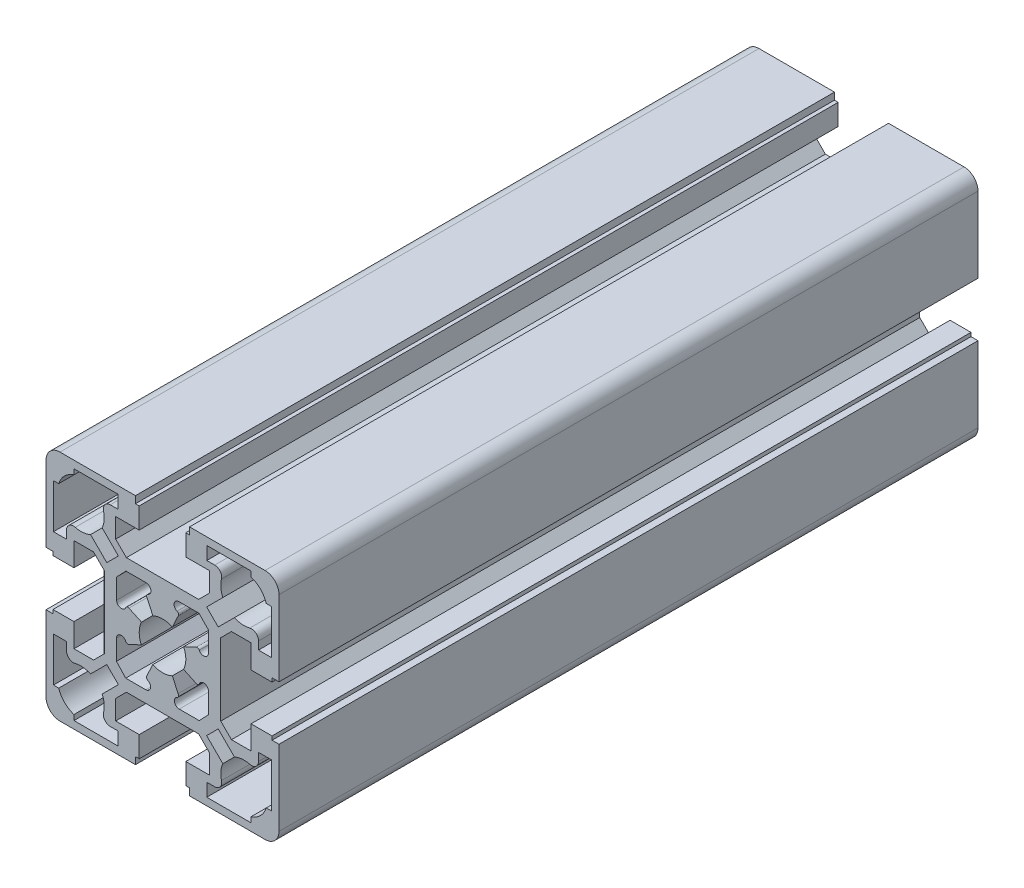
SolidWorks part; units mm, degrees
material "6063-T6"
ref_plane "Front Plane" through (0, 0, 0) normal (0, 0, 1) x (1, 0, 0)
ref_plane "Top Plane" through (0, 0, 0) normal (0, 1, 0) x (1, 0, 0)
ref_plane "Right Plane" through (0, 0, 0) normal (1, 0, 0) x (0, 0, -1)
sketch "Sketch1" plane through (0, 0, 0) normal (0, 0, 1) x (1, 0, 0)
  line L0 (3.5053, 9.9658) -> (7.8227, 9.9658)
  line L1 (7.75, 12.5) -> (-7.75, 12.5)
  line L2 (7.9026, -9.9658) -> (3.5852, -9.9658)
  line L3 (-7.75, -12.5) -> (7.75, -12.5)
  line L4 (10.05, -19) -> (5, -19)
  line L5 (5.8, -25) -> (22, -25)
  line L6 (22, 25) -> (5.8, 25)
  line L7 (5, 19) -> (10.05, 19)
  line L8 (-10.05, -19) -> (-10.05, -14.8)
  line L9 (-25, -5.8) -> (-25, -22)
  line L10 (-23.4, -19) -> (-23.4, -9.5)
  line L11 (-22, -25) -> (-5.8, -25)
  line L12 (-9.5, -23.4) -> (-19, -23.4)
  line L13 (-19, -23.4) -> (-19, -22.2697)
  line L14 (-22.2697, -19) -> (-23.4, -19)
  line L15 (5, -19) -> (5, -23.5)
  line L16 (-5, -23.5) -> (-5, -19)
  line L17 (-9.5, -20.6) -> (-9.5, -23.4)
  line L18 (-5.8, -25) -> (-5.8, -23.5)
  line L19 (-5.8, -23.5) -> (-5, -23.5)
  line L20 (5, -23.5) -> (5.8, -23.5)
  line L21 (5.8, -23.5) -> (5.8, -25)
  line L22 (-5, -19) -> (-10.05, -19)
  line L23 (-11.1998, -20.6) -> (-9.5, -20.6)
  line L24 (2.1096, 4.5332) -> (3.3653, 7.2261)
  line L25 (-9.8504, 3.5503) -> (-9.8596, 7.8676)
  line L26 (-3.3235, 7.2452) -> (-2.062, 4.555)
  line L27 (-19, 5) -> (-19, 10.05)
  line L28 (-25, 22) -> (-25, 5.8)
  line L29 (-12.5, 7.75) -> (-12.5, -7.75)
  line L30 (3.3653, -7.2261) -> (2.1096, -4.5332)
  line L31 (-9.8795, -7.8254) -> (-9.8704, -3.5081)
  line L32 (-2.0907, -4.5419) -> (-3.3521, -7.2322)
  line L33 (-12.5, -7.75) -> (-14.8, -10.05)
  line L34 (-15.4339, -12.9467) -> (-11.9554, -9.4681)
  line L35 (-20.6, -9.5) -> (-20.6, -11.1998)
  line L36 (-23.5, -5.8) -> (-25, -5.8)
  line L37 (-14.8, -10.05) -> (-19, -10.05)
  line L38 (-19, -10.05) -> (-19, -5)
  line L39 (-23.5, -5) -> (-23.5, -5.8)
  line L40 (-19, -5) -> (-23.5, -5)
  line L41 (-23.4, -9.5) -> (-20.6, -9.5)
  line L42 (-11.9554, -9.4681) -> (-9.4681, -11.9554)
  line L43 (-10.05, -14.8) -> (-7.75, -12.5)
  line L44 (-9.4681, -11.9554) -> (-12.9467, -15.4339)
  line L45 (-3.5804, -9.9658) -> (-7.8977, -9.9658)
  line L46 (-7.8977, -9.9658) -> (-9.8795, -7.8254)
  line L47 (-3.1727, -7.9957) -> (-3.1444, -8.009)
  line L48 (3.1496, -8.0006) -> (3.1815, -7.9857)
  line L49 (-25, 5.8) -> (-23.5, 5.8)
  line L50 (-23.5, 5.8) -> (-23.5, 5)
  line L51 (-23.5, 5) -> (-19, 5)
  line L52 (-7.9125, -3.0762) -> (-7.8928, -3.1186)
  line L53 (-7.2283, -3.3604) -> (-4.5354, -2.1047)
  line L54 (4.5262, -2.1244) -> (7.2218, -3.3744)
  line L55 (-4.5157, 2.1468) -> (-7.2086, 3.4025)
  line L56 (-7.873, 3.1607) -> (-7.8927, 3.1184)
  line L57 (7.2314, 3.3538) -> (4.5359, 2.1038)
  line L58 (-10.05, 14.8) -> (-10.05, 19)
  line L59 (-23.4, 9.5) -> (-23.4, 19)
  line L60 (-14.8, 10.05) -> (-12.5, 7.75)
  line L61 (-11.9554, 9.4681) -> (-15.4339, 12.9467)
  line L62 (-19, 10.05) -> (-14.8, 10.05)
  line L63 (-20.6, 11.1998) -> (-20.6, 9.5)
  line L64 (-20.6, 9.5) -> (-23.4, 9.5)
  line L65 (-7.75, 12.5) -> (-10.05, 14.8)
  line L66 (-12.9467, 15.4339) -> (-9.4681, 11.9554)
  line L67 (-9.8596, 7.8676) -> (-7.8332, 9.9658)
  line L68 (-7.8332, 9.9658) -> (-3.5158, 9.9658)
  line L69 (-3.0799, 8.009) -> (-3.1275, 7.9867)
  line L70 (-9.4681, 11.9554) -> (-11.9554, 9.4681)
  line L71 (3.164, 7.9635) -> (3.073, 8.0057)
  line L72 (-5.8, 25) -> (-22, 25)
  line L73 (-19, 23.4) -> (-9.5, 23.4)
  line L74 (-19, 22.2697) -> (-19, 23.4)
  line L75 (-23.4, 19) -> (-22.2697, 19)
  line L76 (5.8, 25) -> (5.8, 23.5)
  line L77 (-5.8, 23.5) -> (-5.8, 25)
  line L78 (-10.05, 19) -> (-5, 19)
  line L79 (-5, 19) -> (-5, 23.5)
  line L80 (-5, 23.5) -> (-5.8, 23.5)
  line L81 (-9.5, 23.4) -> (-9.5, 20.6)
  line L82 (-9.5, 20.6) -> (-11.1998, 20.6)
  line L83 (5.8, 23.5) -> (5, 23.5)
  line L84 (5, 23.5) -> (5, 19)
  line L85 (25, -22) -> (25, -5.8)
  line L86 (23.4, -9.5) -> (23.4, -19)
  line L87 (10.05, -14.8) -> (10.05, -19)
  line L88 (9.5, -23.4) -> (9.5, -20.6)
  line L89 (19, -23.4) -> (9.5, -23.4)
  line L90 (19, -22.2697) -> (19, -23.4)
  line L91 (9.5, -20.6) -> (11.1998, -20.6)
  line L92 (23.4, -19) -> (22.2697, -19)
  line L93 (25, 5.8) -> (25, 22)
  line L94 (19, 10.05) -> (19, 5)
  line L95 (9.8596, 7.8778) -> (9.8504, 3.5605)
  line L96 (12.5, -7.75) -> (12.5, 7.75)
  line L97 (9.873, -3.5146) -> (9.8913, -7.8318)
  line L98 (20.6, -11.1998) -> (20.6, -9.5)
  line L99 (9.4681, -11.9554) -> (11.9554, -9.4681)
  line L100 (11.9554, -9.4681) -> (15.4339, -12.9467)
  line L101 (12.9467, -15.4339) -> (9.4681, -11.9554)
  line L102 (7.75, -12.5) -> (10.05, -14.8)
  line L103 (19, -10.05) -> (14.8, -10.05)
  line L104 (14.8, -10.05) -> (12.5, -7.75)
  line L105 (9.8913, -7.8318) -> (7.9026, -9.9658)
  line L106 (25, -5.8) -> (23.5, -5.8)
  line L107 (23.5, -5.8) -> (23.5, -5)
  line L108 (20.6, -9.5) -> (23.4, -9.5)
  line L109 (19, -5) -> (19, -10.05)
  line L110 (23.5, -5) -> (19, -5)
  line L111 (7.8857, -3.1312) -> (7.907, -3.0853)
  line L112 (7.8866, 3.1295) -> (7.8954, 3.1106)
  line L113 (23.5, 5) -> (23.5, 5.8)
  line L114 (23.5, 5.8) -> (25, 5.8)
  line L115 (19, 5) -> (23.5, 5)
  line L116 (23.4, 19) -> (23.4, 9.5)
  line L117 (10.05, 19) -> (10.05, 14.8)
  line L118 (9.4681, 11.9554) -> (12.9467, 15.4339)
  line L119 (15.4339, 12.9467) -> (11.9554, 9.4681)
  line L120 (10.05, 14.8) -> (7.75, 12.5)
  line L121 (14.8, 10.05) -> (19, 10.05)
  line L122 (12.5, 7.75) -> (14.8, 10.05)
  line L123 (11.9554, 9.4681) -> (9.4681, 11.9554)
  line L124 (7.8227, 9.9658) -> (9.8596, 7.8778)
  line L125 (23.4, 9.5) -> (20.6, 9.5)
  line L126 (20.6, 9.5) -> (20.6, 11.1998)
  line L127 (9.5, 23.4) -> (19, 23.4)
  line L128 (11.1998, 20.6) -> (9.5, 20.6)
  line L129 (9.5, 20.6) -> (9.5, 23.4)
  line L130 (22.2697, 19) -> (23.4, 19)
  line L131 (19, 23.4) -> (19, 22.2697)
  line L132 (0, 33.4874) -> (0, -33.1097) construction
  line L133 (-40.5374, 0) -> (39.9079, 0) construction
  arc A0 (7.8954, 3.1106) -> (7.2314, 3.3538) centre (7.4418, 2.9002) ccw
  arc A1 (7.2218, -3.3744) -> (7.8857, -3.1312) centre (7.4321, -2.9208) ccw
  arc A2 (-12.6537, -18.7308) -> (-12.9467, -15.4339) centre (-17.5, -17.5) ccw
  arc A3 (-22.2697, -19) -> (-19, -22.2697) centre (-17.5, -17.5) ccw
  arc A4 (-25, -22) -> (-22, -25) centre (-22, -22) ccw
  arc A5 (-12.6537, -18.7308) -> (-11.1998, -20.6) centre (-11.1998, -19.1) ccw
  arc A6 (-2.0907, -4.5419) -> (2.1096, -4.5332) centre (0, 0) ccw
  arc A7 (-20.6, -11.1998) -> (-18.7308, -12.6537) centre (-19.1, -11.1998) ccw
  arc A8 (-15.4339, -12.9467) -> (-18.7308, -12.6537) centre (-17.5, -17.5) ccw
  arc A9 (-3.5804, -9.9658) -> (-3.1444, -8.009) centre (-3.5804, -8.9388) ccw
  arc A10 (-3.3521, -7.2322) -> (-3.1727, -7.9957) centre (-2.9605, -7.543) ccw
  arc A11 (3.1496, -8.0006) -> (3.5852, -9.9658) centre (3.5852, -8.9349) ccw
  arc A12 (3.1815, -7.9857) -> (3.3653, -7.2261) centre (2.9702, -7.5325) ccw
  arc A13 (-4.5157, 2.1468) -> (-4.5354, -2.1047) centre (0, 0) ccw
  arc A14 (4.5262, -2.1244) -> (4.5359, 2.1038) centre (0, 0) ccw
  arc A15 (-7.9125, -3.0762) -> (-9.8704, -3.5081) centre (-8.8434, -3.5103) ccw
  arc A16 (-7.8928, -3.1186) -> (-7.2283, -3.3604) centre (-7.4396, -2.9073) ccw
  arc A17 (-7.2086, 3.4025) -> (-7.873, 3.1607) centre (-7.4199, 2.9494) ccw
  arc A18 (-9.8504, 3.5503) -> (-7.8927, 3.1184) centre (-8.8235, 3.5524) ccw
  arc A19 (2.1096, 4.5332) -> (-2.062, 4.555) centre (0, 0) ccw
  arc A20 (-12.9467, 15.4339) -> (-12.6537, 18.7308) centre (-17.5, 17.5) ccw
  arc A21 (-18.7308, 12.6537) -> (-15.4339, 12.9467) centre (-17.5, 17.5) ccw
  arc A22 (-18.7308, 12.6537) -> (-20.6, 11.1998) centre (-19.1, 11.1998) ccw
  arc A23 (-3.0799, 8.009) -> (-3.5158, 9.9658) centre (-3.5158, 8.9388) ccw
  arc A24 (-3.1275, 7.9867) -> (-3.3235, 7.2452) centre (-2.9152, 7.534) ccw
  arc A25 (3.3653, 7.2261) -> (3.164, 7.9635) centre (2.9536, 7.5099) ccw
  arc A26 (3.5053, 9.9658) -> (3.073, 8.0057) centre (3.5053, 8.9381) ccw
  arc A27 (-22, 25) -> (-25, 22) centre (-22, 22) ccw
  arc A28 (-19, 22.2697) -> (-22.2697, 19) centre (-17.5, 17.5) ccw
  arc A29 (-11.1998, 20.6) -> (-12.6537, 18.7308) centre (-11.1998, 19.1) ccw
  arc A30 (12.9467, -15.4339) -> (12.6537, -18.7308) centre (17.5, -17.5) ccw
  arc A31 (22, -25) -> (25, -22) centre (22, -22) ccw
  arc A32 (19, -22.2697) -> (22.2697, -19) centre (17.5, -17.5) ccw
  arc A33 (11.1998, -20.6) -> (12.6537, -18.7308) centre (11.1998, -19.1) ccw
  arc A34 (18.7308, -12.6537) -> (15.4339, -12.9467) centre (17.5, -17.5) ccw
  arc A35 (18.7308, -12.6537) -> (20.6, -11.1998) centre (19.1, -11.1998) ccw
  arc A36 (9.873, -3.5146) -> (7.907, -3.0853) centre (8.8422, -3.5189) ccw
  arc A37 (7.8866, 3.1295) -> (9.8504, 3.5605) centre (8.8207, 3.5626) ccw
  arc A38 (12.6537, 18.7308) -> (12.9467, 15.4339) centre (17.5, 17.5) ccw
  arc A39 (15.4339, 12.9467) -> (18.7308, 12.6537) centre (17.5, 17.5) ccw
  arc A40 (20.6, 11.1998) -> (18.7308, 12.6537) centre (19.1, 11.1998) ccw
  arc A41 (25, 22) -> (22, 25) centre (22, 22) ccw
  arc A42 (12.6537, 18.7308) -> (11.1998, 20.6) centre (11.1998, 19.1) ccw
  arc A43 (22.2697, 19) -> (19, 22.2697) centre (17.5, 17.5) ccw
  dimension "D3" = 10
  dimension "D1" = 50
  dimension "D2" = 50
  dimension "D4" = 10
  dimension "D5" = 10
extrude "Base-Extrude" add sketch "Sketch1" against normal blind 150
